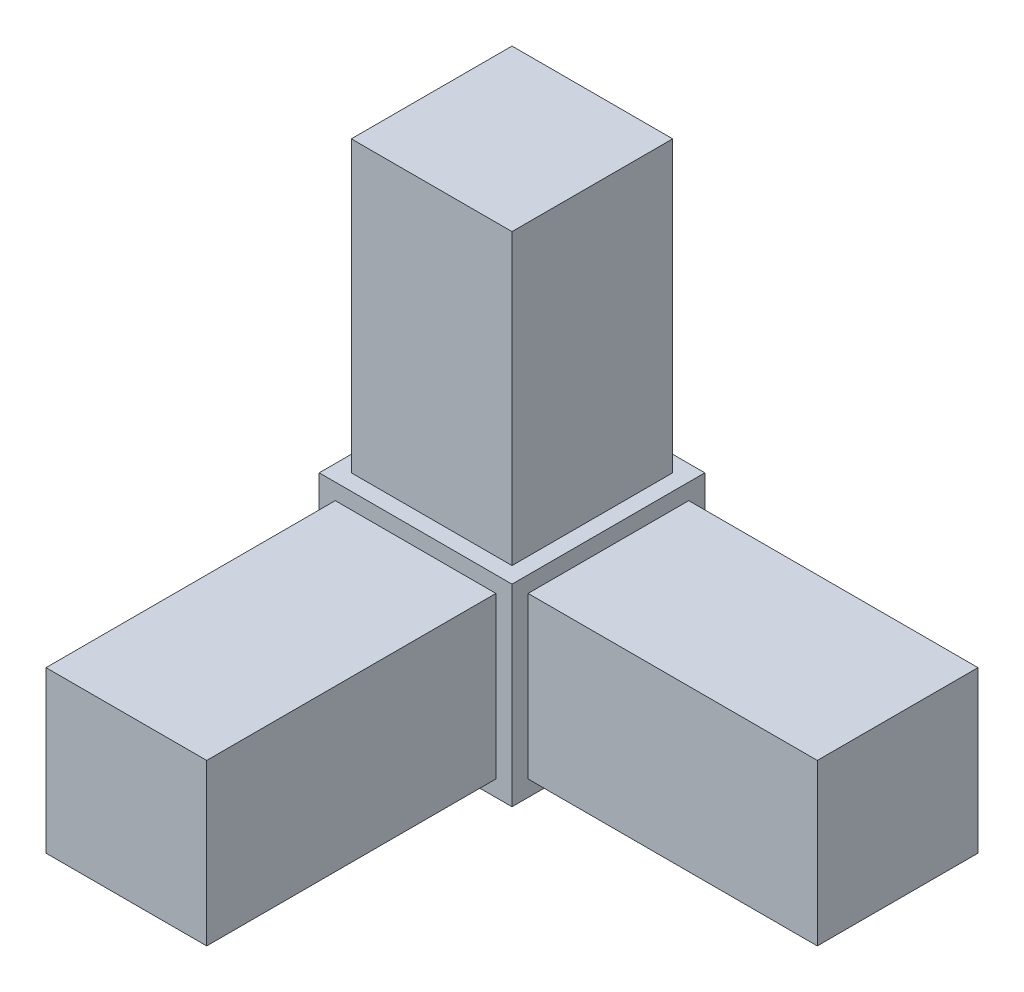
SolidWorks part; units mm, degrees
material "ABS"
ref_plane "Front Plane" through (0, 0, 0) normal (0, 0, 1) x (1, 0, 0)
ref_plane "Top Plane" through (0, 0, 0) normal (0, 1, 0) x (1, 0, 0)
ref_plane "Right Plane" through (0, 0, 0) normal (1, 0, 0) x (0, 0, -1)
sketch "Sketch1" plane through (0, 0, 0) normal (0, 0, 1) x (1, 0, 0)
  line L1 (9.525, -9.525) -> (-9.525, -9.525)
  line L2 (9.525, -9.525) -> (9.525, 9.525)
  line L3 (9.525, 9.525) -> (-9.525, 9.525)
  line L4 (-9.525, -9.525) -> (-9.525, 9.525)
  line L5 (9.525, -9.525) -> (-9.525, 9.525) construction
  line L6 (9.525, 9.525) -> (-9.525, -9.525) construction
  point P0 (0, 0)
  dimension "D1" = 19.05
extrude "Boss-Extrude1" add sketch "Sketch1" along normal blind 19.05
sketch "Sketch2" plane through (0, 9.525, 0) normal (0, 1, 0) x (1, 0, 0)
  line L0 (-9.525, 0) -> (9.525, -19.05) construction
  line L2 (-7.9375, -1.5875) -> (7.9375, -1.5875)
  line L3 (-7.9375, -1.5875) -> (-7.9375, -17.4625)
  line L4 (-7.9375, -17.4625) -> (7.9375, -17.4625)
  line L5 (7.9375, -1.5875) -> (7.9375, -17.4625)
  line L6 (-7.9375, -1.5875) -> (7.9375, -17.4625) construction
  line L7 (-7.9375, -17.4625) -> (7.9375, -1.5875) construction
  point P4 (0, -9.525)
  dimension "D1" = 15.875
extrude "Boss-Extrude2" add sketch "Sketch2" along normal blind 28.575
sketch "Sketch3" plane through (9.525, 0, 0) normal (1, 0, 0) x (0, 0, -1)
  line L0 (-19.05, 9.525) -> (0, -9.525) construction
  line L2 (-17.4625, -7.9375) -> (-1.5875, -7.9375)
  line L3 (-17.4625, -7.9375) -> (-17.4625, 7.9375)
  line L4 (-17.4625, 7.9375) -> (-1.5875, 7.9375)
  line L5 (-1.5875, -7.9375) -> (-1.5875, 7.9375)
  line L6 (-17.4625, -7.9375) -> (-1.5875, 7.9375) construction
  line L7 (-17.4625, 7.9375) -> (-1.5875, -7.9375) construction
  point P4 (-9.525, 0)
  dimension "D1" = 15.875
extrude "Boss-Extrude3" add sketch "Sketch3" along normal blind 28.575
sketch "Sketch4" plane through (0, 0, 19.05) normal (0, 0, 1) x (1, 0, 0)
  line L0 (-9.525, 9.525) -> (9.525, -9.525) construction
  line L2 (7.9375, -7.9375) -> (-7.9375, -7.9375)
  line L3 (7.9375, -7.9375) -> (7.9375, 7.9375)
  line L4 (7.9375, 7.9375) -> (-7.9375, 7.9375)
  line L5 (-7.9375, -7.9375) -> (-7.9375, 7.9375)
  line L6 (7.9375, -7.9375) -> (-7.9375, 7.9375) construction
  line L7 (7.9375, 7.9375) -> (-7.9375, -7.9375) construction
  point P4 (0, 0)
  dimension "D1" = 15.875
extrude "Boss-Extrude4" add sketch "Sketch4" along normal blind 28.575
equation "\"Height\"= 32in"
equation "\"Width\"= 23in"
equation "\"Depth\"= 20in"
equation "\"Plexi\"= .121in"
equation "\"MagnetThickness\"= .125in"
equation "\"MagnetDiameter\"= 12mm"
equation "\"DoorPlexi\"= \"Plexi\""
equation "\"BasePlateThickness\"= 0.5in"
equation "\"BasePlateWidth\"= \"Width\"+\"EBWidth\"-2*\"Plexi\""
equation "\"BasePlateDepth\"= \"TopBarDepth\"+2*\"CornerCube\""
equation "\"Boxsize\"= .75in"
equation "\"Boxinner\"= .625in"
equation "\"CornerCube\"= 0.75in"
equation "\"FingerLength\"= 1.125in"
equation "\"Cutwidth\"= .016in"
equation "\"Earsize\"= 1in + \"Cutwidth\" /2"
equation "\"Slotsize\"= 1in - \"Cutwidth\" / 2"
equation "\"InnerWidth\"= \"Width\" - 2* \"Plexi\""
equation "\"InnerHeight\"= \"Height\" -2 * \"Plexi\""
equation "\"InnerDepth\"= \"Depth\" - 2*\"Plexi\""
equation "\"RearNumHoles\"= 4"
equation "\"RearHolesBorder\"= 2.25"
equation "\"RearHoleSpacing\"= (\"Width\" - 2*\"RearHolesBorder\") / (\"RearNumHoles\"-1)"
equation "\"RearBarLength\"= (\"InnerWidth\"-2*\"CornerCube\")"
equation "\"RearTopNumHoles\"= 4"
equation "\"RearTopHolesBorder\"= 3.1"
equation "\"RearTopHolesSpacing\"= (\"Width\" - 2*\"RearTopHolesBorder\") / (\"RearTopNumHoles\"-1)"
equation "\"SideTopNumHoles\"= 4"
equation "\"SideTopHoleOffset\"=\"CornerCube\"+\"FingerLength\"+\"Plexi\"+.5"
equation "\"SideTopHoleSpacing\"= (\"TopBarDepth\"-2*\"SideTopHoleOffset\") / (\"SideTopNumHoles\"-1)"
equation "\"SideHorizNumHoles\"= 4"
equation "\"SideHorizHoleBorder\"= 1.50"
equation "\"SideHorizHoleSpacing\"= (\"TopBarDepth\"-2*\"SideHorizHoleBorder\") / (\"SideHorizNumHoles\"-1)"
equation "\"SideVertBarLength\"=\"Height\"-\"BasePlateThickness\"-2*\"CornerCube\"-\"Plexi\""
equation "\"SideVertNumHoles\"= 4"
equation "\"SideVertHolesBorder\"= \"CornerCube\"+\"FingerLength\"+1.50"
equation "\"SideVertHoleSpacing\"= (\"InnerHeight\" - 2*\"SideVertHolesBorder\") / (\"SideVertNumHoles\"-1)"
equation "\"RearSideVertNumHoles\"= 4"
equation "\"RearSideVertHolesBorder\"= 2.4"
equation "\"RearSideVertHoleSpacing\"= (\"InnerHeight\" - 2*\"RearSideVertHolesBorder\") / (\"RearSideVertNumHoles\"-1)"
equation "\"RivetDia\"= .228in"
equation "\"SlotDepth\"= \"Plexi\" + 0.75in + .005in"
equation "\"SideSlotWidth\"= \"Plexi\"+.005in"
equation "\"SidePanelVertSpacing\"= (\"Height\"-2*(1.75-\"Plexi\")) / 5"
equation "\"BottomPanelSideHoleSpacing\"= (\"InnerDepth\"-2*(1.75-\"Plexi\")) / 4"
equation "\"FrontDoorGap\"= .1in"
equation "\"TopDepth\"= \"Depth\"-\"DoorPlexi\"-\"FrontDoorGap\""
equation "\"TopBarDepth\"= \"Depth\"-\"DoorPlexi\"-\"Plexi\"-2*\"MagnetThickness\"-2*\"CornerCube\""
equation "\"D1@Boss-Extrude1\"=\"CornerCube\""
equation "\"D1@Sketch1\"=\"CornerCube\""
equation "\"D1@Boss-Extrude4\"=\"FingerLength\""
equation "\"D1@Boss-Extrude3\"=\"FingerLength\""
equation "\"D1@Boss-Extrude2\"=\"FingerLength\""
equation "\"D1@Sketch2\"=\"Boxinner\""
equation "\"D1@Sketch3\"=\"Boxinner\""
equation "\"D1@Sketch4\"=\"Boxinner\""
